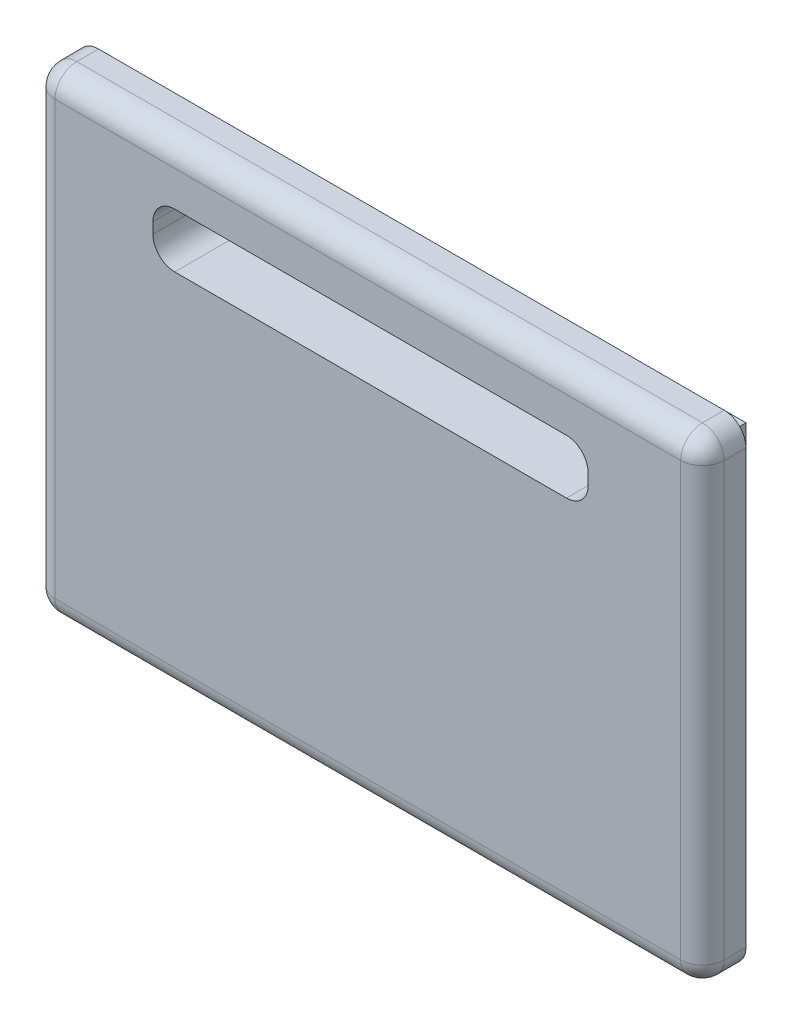
SolidWorks part; units mm, degrees
ref_plane "Plan de face" through (0, 0, 0) normal (0, 0, 1) x (1, 0, 0)
ref_plane "Plan de dessus" through (0, 0, 0) normal (0, 1, 0) x (1, 0, 0)
ref_plane "Plan de droite" through (0, 0, 0) normal (1, 0, 0) x (0, 0, -1)
sketch "Esquisse1" plane through (0, 0, 0) normal (0, 0, 1) x (1, 0, 0)
  line L1 (-21.5227, 22.815) -> (39.9773, 22.815)
  line L2 (-21.5227, 22.815) -> (-21.5227, -20.935)
  line L3 (-21.5227, -20.935) -> (39.9773, -20.935)
  line L4 (39.9773, 22.815) -> (39.9773, -20.935)
  dimension "D1" = 61.5
  dimension "D2" = 43.75
extrude "Boss.-Extru.1" add sketch "Esquisse1" along normal blind 4
sketch "Esquisse2" plane through (0, 0, 0) normal (0, 0, -1) x (-1, 0, 0)
  line L0 (21.5227, -20.935) -> (-39.9773, -20.935) construction
  line L1 (17.5227, -16.935) -> (-35.9773, -16.935)
  line L2 (17.5227, -16.935) -> (17.5227, 18.815)
  line L3 (17.5227, 18.815) -> (-35.9773, 18.815)
  line L4 (-35.9773, -16.935) -> (-35.9773, 18.815)
  line L5 (21.5227, 22.815) -> (21.5227, -20.935) construction
  dimension "D1" = 53.5
  dimension "D2" = 35.75
  dimension "D3" = 4
  dimension "D4" = 4
extrude "Boss.-Extru.2" add sketch "Esquisse2" along normal blind 4
fillet "Congé1" radius 2 8 edges at (9.2273, 22.815, 4) (39.9773, 0.94, 4) (9.2273, -20.935, 4) (-21.5227, 0.94, 4) (-21.5227, 22.815, 2) (-21.5227, -20.935, 2) (39.9773, -20.935, 2) (39.9773, 22.815, 2)
sketch "Esquisse3" plane through (0, 0, 4) normal (0, 0, 1) x (1, 0, 0)
  line L0 (-19.5227, 20.815) -> (-19.5227, -18.935) construction
  line L1 (-10.5227, 17.5722) -> (29.4773, 17.5722)
  line L2 (-10.5227, 17.5722) -> (-10.5227, 12.5722)
  line L3 (-10.5227, 12.5722) -> (29.4773, 12.5722)
  line L4 (29.4773, 17.5722) -> (29.4773, 12.5722)
  dimension "D1" = 40
  dimension "D2" = 5
  dimension "D3" = 9
extrude "Enlèv. mat.-Extru.1" cut sketch "Esquisse3" against normal up to next
fillet "Congé2" radius 2 4 edges at (-10.5227, 12.5722, 0) (-10.5227, 17.5722, 0) (29.4773, 12.5722, 0) (29.4773, 17.5722, 0)
